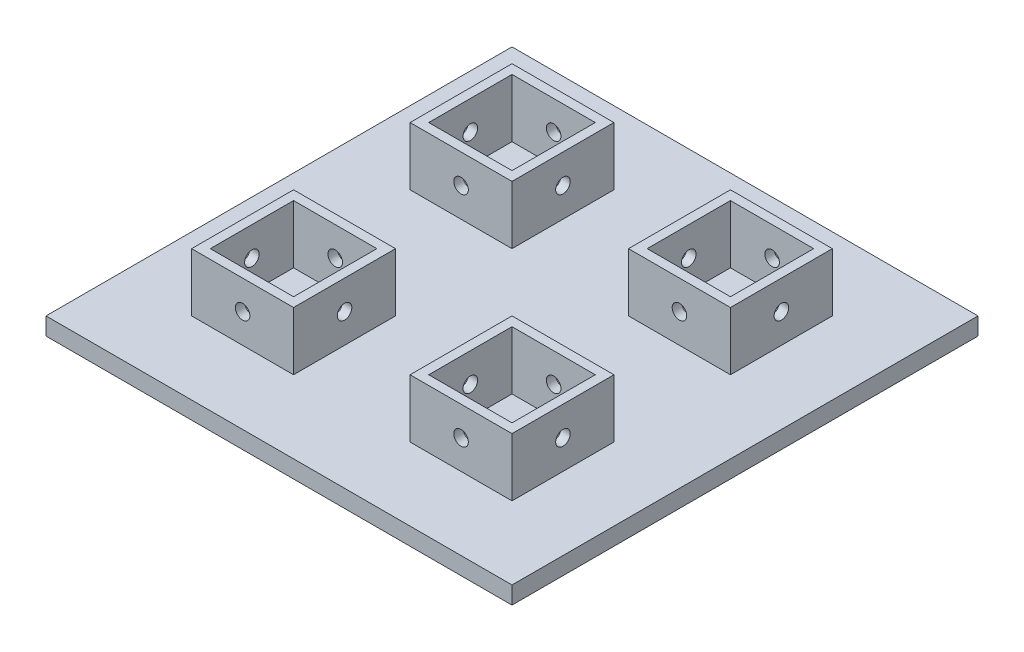
SolidWorks part; units mm, degrees
ref_plane "Front Plane" through (0, 0, 0) normal (0, 0, 1) x (1, 0, 0)
ref_plane "Top Plane" through (0, 0, 0) normal (0, 1, 0) x (1, 0, 0)
ref_plane "Right Plane" through (0, 0, 0) normal (1, 0, 0) x (0, 0, -1)
sketch "Sketch1" plane through (0, 0, 0) normal (0, 1, 0) x (1, 0, 0)
  line L1 (-40, -40) -> (40, -40)
  line L2 (-40, -40) -> (-40, 40)
  line L3 (-40, 40) -> (40, 40)
  line L4 (40, -40) -> (40, 40)
  line L5 (-40, -40) -> (40, 40) construction
  line L6 (-40, 40) -> (40, -40) construction
  point P0 (0, 0)
  dimension "D1" = 80
  dimension "D2" = 80
extrude "Boss-Extrude1" add sketch "Sketch1" along normal blind 3
sketch "Sketch2" plane through (0, 3, 0) normal (0, 1, 0) x (1, 0, 0)
  line L0 (-10, 10) -> (0, 0) construction
  line L1 (-27.5, 27.5) -> (-10, 27.5)
  line L2 (-27.5, 27.5) -> (-27.5, 10)
  line L3 (-27.5, 10) -> (-10, 10)
  line L4 (-10, 27.5) -> (-10, 10)
  line L5 (-27.5, 27.5) -> (-10, 10) construction
  line L6 (-27.5, 10) -> (-10, 27.5) construction
  line L7 (0, 0) -> (-10, 0) construction
  line L8 (-10, 0) -> (-10, 10) construction
  point P0 (-18.75, 18.75)
  point P5 (-13.6071, 0)
  point P9 (-30.7657, 30.7657)
  point P10 (-15.8011, 0)
  dimension "D1" = 45
  dimension "D2" = 17.5
  dimension "D3" = 17.5
  dimension "D4" = 10
extrude "Boss-Extrude2" add sketch "Sketch2" along normal blind 10
sketch "Sketch3" plane through (0, 13, 0) normal (0, 1, 0) x (1, 0, 0)
  line L8 (-11.6, 11.6) -> (-11.6, 25.9)
  line L9 (-11.6, 25.9) -> (-25.9, 25.9)
  line L10 (-25.9, 25.9) -> (-25.9, 11.6)
  line L11 (-25.9, 11.6) -> (-11.6, 11.6)
  line L12 (-11.6, 11.6) -> (-11.6, 25.9)
  line L13 (-11.6, 25.9) -> (-25.9, 25.9)
  line L14 (-25.9, 25.9) -> (-25.9, 11.6)
  line L15 (-25.9, 11.6) -> (-11.6, 11.6)
  dimension "D1" = 1.6
extrude "Cut-Extrude1" cut sketch "Sketch3" against normal up to surface (10 mm away) up to face at (0, 3, 0)
hole_wizard "Tap Drill for M3x0.5 Tap1" positions "Sketch4" profile "Sketch5" hole size "M3x0.5" standard "ANSI Metric" end condition through all
sketch "Sketch4" plane through (0, 0, -10) normal (0, 0, 1) x (1, 0, 0)
  line L0 (-27.5, 13) -> (-10, 3) construction
  point P0 (-18.75, 8)
  point P9 (0, 0)
  point P10 (-18.75, 8)
sketch "Sketch5" plane through (-18.75, 8, -10) normal (1, 0, 0) x (0, -1, 0)
  line L0 (0, 0) -> (0, 30)
  line L1 (0, 30) -> (1.25, 30)
  line L2 (1.25, 30) -> (1.25, 0)
  line L5 (1.25, 0) -> (0, 0)
  line L11 (0, -6.35) -> (0, 107.95) construction
  dimension "Thru Hole Dia." = 2.5
  dimension "Thru Hole Depth" = 30
hole_wizard "Tap Drill for M3x0.5 Tap2" positions "Sketch6" profile "Sketch7" hole size "M3x0.5" standard "ANSI Metric" end condition through all
sketch "Sketch6" plane through (-27.5, 0, 0) normal (-1, 0, 0) x (0, 0, 1)
  line L0 (-27.5, 13) -> (-10, 3) construction
  point P7 (-18.75, 8)
sketch "Sketch7" plane through (-27.5, 8, -18.75) normal (0, 1, 0) x (0, 0, 1)
  line L0 (0, 0) -> (0, 67.5)
  line L1 (0, 67.5) -> (1.25, 67.5)
  line L2 (1.25, 67.5) -> (1.25, 0)
  line L5 (1.25, 0) -> (0, 0)
  line L11 (0, -6.35) -> (0, 107.95) construction
  dimension "Thru Hole Dia." = 2.5
  dimension "Thru Hole Depth" = 67.5
ref_plane "Plane1" through (0, 0, 0) normal (-1, 0, 0) x (0, 0, 1)
ref_plane "Plane2" through (0, 0, 0) normal (0, 0, 1) x (1, 0, 0)
mirror "Mirror1" about plane through (0, 0, 0) normal (-1, 0, 0) of "Cut-Extrude1", "Tap Drill for M3x0.5 Tap1", "Tap Drill for M3x0.5 Tap2", "Boss-Extrude2"
mirror "Mirror2" about plane through (0, 0, 0) normal (0, 0, 1) of "Mirror1", "Boss-Extrude2", "Cut-Extrude1", "Tap Drill for M3x0.5 Tap1", "Tap Drill for M3x0.5 Tap2"
